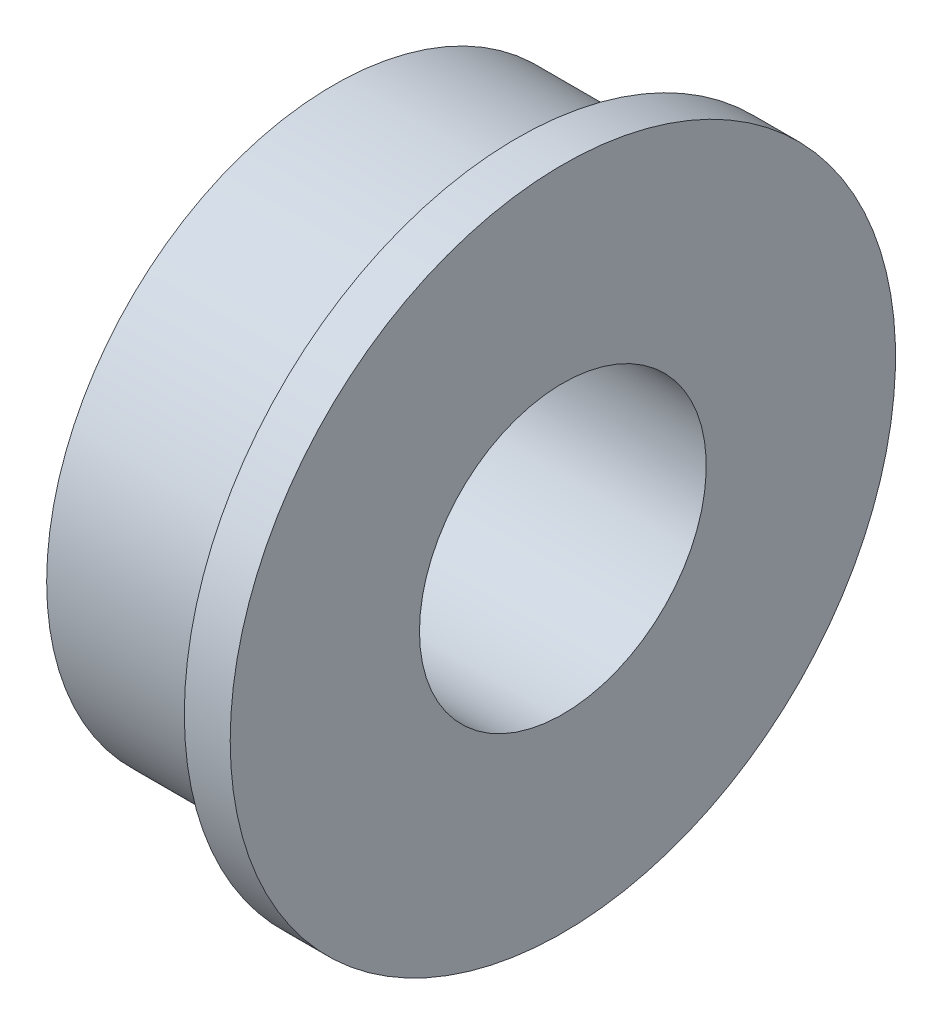
SolidWorks part; units mm, degrees
material "Alloy Steel"
ref_plane "Front Plane" through (0, 0, 0) normal (0, 0, 1) x (1, 0, 0)
ref_plane "Top Plane" through (0, 0, 0) normal (0, 1, 0) x (1, 0, 0)
ref_plane "Right Plane" through (0, 0, 0) normal (1, 0, 0) x (0, 0, -1)
sketch "Sketch1" plane through (0, 0, 0) normal (0, 0, 1) x (1, 0, 0)
  line L0 (-7.8722, 0) -> (8.7616, 0) construction
  line L1 (-2, 5) -> (-2, 2.5)
  line L2 (-2, 2.5) -> (2, 2.5)
  line L3 (2, 2.5) -> (2, 5.8)
  line L4 (2, 5.8) -> (1.2, 5.8)
  line L5 (1.2, 5.8) -> (1.2, 5)
  line L6 (1.2, 5) -> (-2, 5)
  line L7 (0, 0) -> (0, 8.7206) construction
  dimension "D1" = 2.5
  dimension "D2" = 5
  dimension "D3" = 4
  dimension "D4" = 5.8
  dimension "D5" = 0.8
revolve "Revolve1" add sketch "Sketch1" angle 360 about L0
